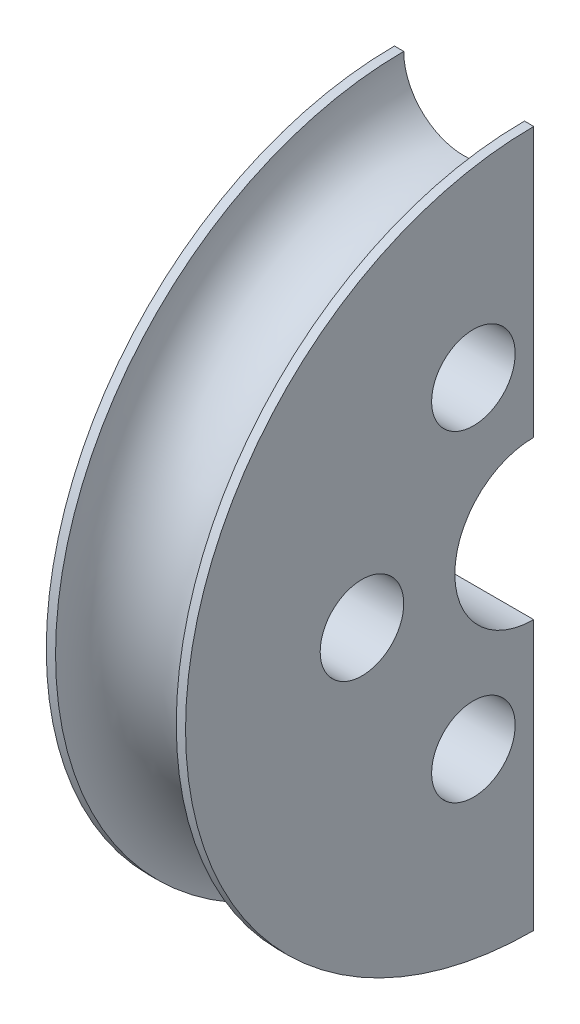
SolidWorks part; units mm, degrees
material "Acier allié"
ref_plane "Plan de face" through (0, 0, 0) normal (0, 0, 1) x (1, 0, 0)
ref_plane "Plan de dessus" through (0, 0, 0) normal (0, 1, 0) x (1, 0, 0)
ref_plane "Plan de droite" through (0, 0, 0) normal (1, 0, 0) x (0, 0, -1)
sketch "Esquisse1" plane through (0, 0, 0) normal (0, 0, 1) x (1, 0, 0)
  line L0 (0, 0) -> (30, 0) construction
  line L1 (0, 17) -> (0, 75)
  line L2 (0, 75) -> (2, 75)
  line L3 (30, 75) -> (30, 17)
  line L4 (28, 75) -> (30, 75)
  line L5 (0, 17) -> (30, 17)
  arc A0 (2, 75) -> (28, 75) centre (15, 75) ccw
  dimension "D1" = 30
  dimension "D2" = 2
  dimension "D3" = 2
  dimension "D4" = 75
  dimension "D5" = 75
  dimension "D6" = 34
revolve "Révolution1" add sketch "Esquisse1" angle 180 about L0
sketch "Esquisse2" plane through (0, 0, 0) normal (-1, 0, 0) x (0, 0, 1)
  line L0 (0, -75) -> (0, -17) construction
  line L1 (0, 75) -> (0, 17) construction
  circle A0 centre (37, 0) radius 9
  circle A1 centre (13, -34.641) radius 9
  circle A2 centre (13, 34.641) radius 9
  dimension "D1" = 18
  dimension "D2" = 18
  dimension "D3" = 18
  dimension "D4" = 13
  dimension "D5" = 13
  dimension "D6" = 37
  dimension "D7" = 37
  dimension "D8" = 37
extrude "Enlèv. mat.-Extru.1" cut sketch "Esquisse2" against normal through all
